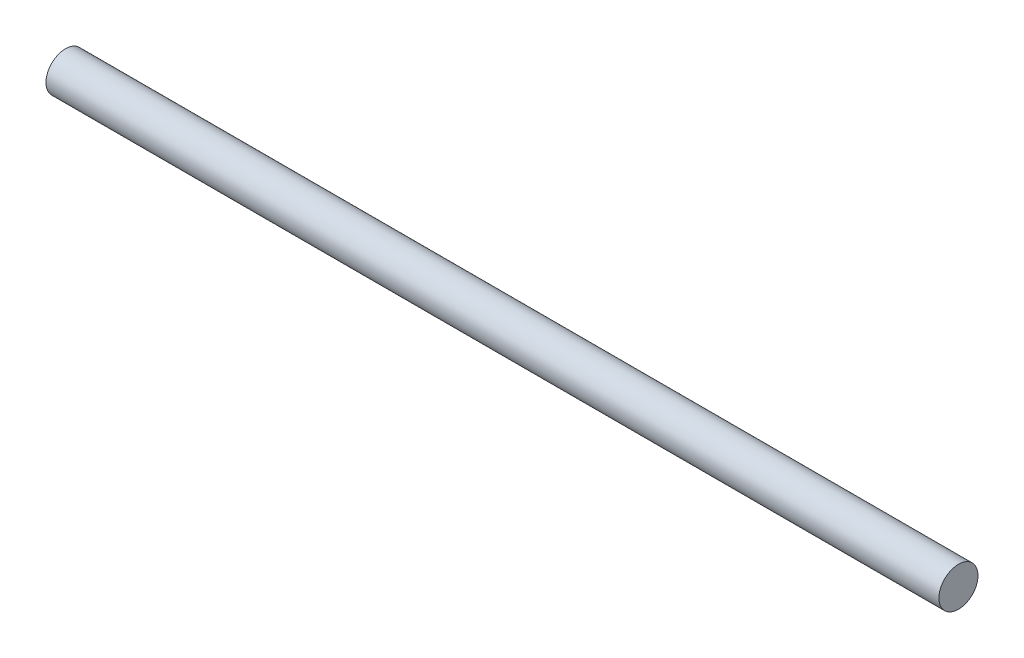
SolidWorks part; units mm, degrees
ref_plane "Front Plane" through (0, 0, 0) normal (0, 0, 1) x (1, 0, 0)
ref_plane "Top Plane" through (0, 0, 0) normal (0, 1, 0) x (1, 0, 0)
ref_plane "Right Plane" through (0, 0, 0) normal (1, 0, 0) x (0, 0, -1)
sketch "Sketch1" plane through (0, 0, 0) normal (1, 0, 0) x (0, 0, -1)
  circle A0 centre (-58.3982, -31.829) radius 3.5
extrude "Boss-Extrude1" add sketch "Sketch1" along normal blind 160
